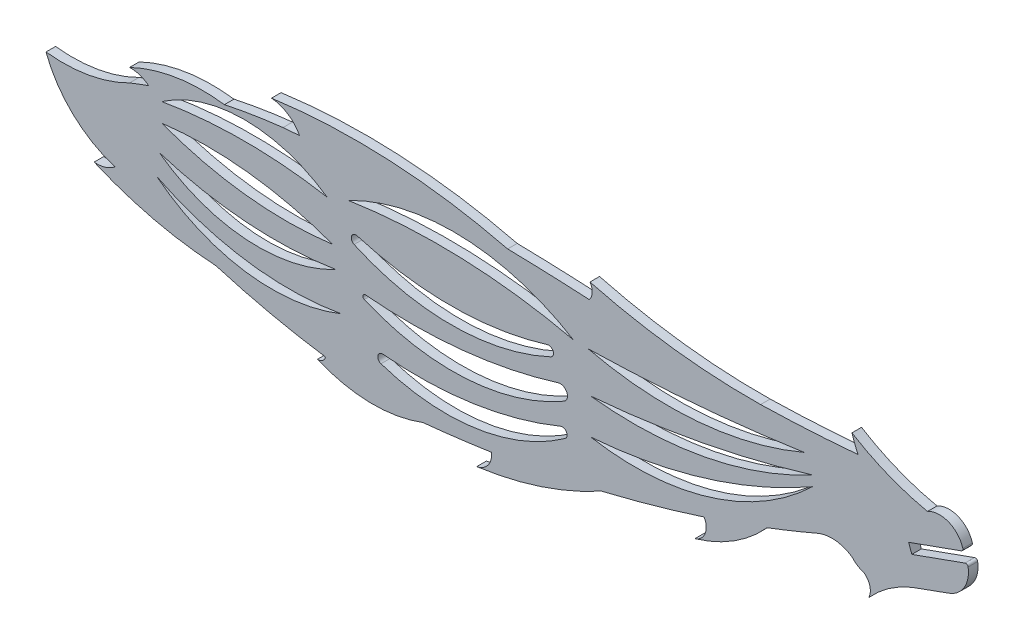
SolidWorks part; units mm, degrees
ref_plane "Front Plane" through (0, 0, 0) normal (0, 0, 1) x (1, 0, 0)
ref_plane "Top Plane" through (0, 0, 0) normal (0, 1, 0) x (1, 0, 0)
ref_plane "Right Plane" through (0, 0, 0) normal (1, 0, 0) x (0, 0, -1)
sketch "Model" plane through (0, 0, 0) normal (0, 0, 1) x (1, 0, 0)
  line L123 (134.9601, 18.3195) -> (129.2015, 16.2312)
  line L124 (129.2015, 20.778) -> (137.684, 23.8208)
  line L125 (137.0994, 25.2113) -> (128.693, 22.1962)
  line L127 (128.693, 22.1962) -> (129.2015, 20.778)
  arc A0 (131.7063, 27.9608) -> (119.655, 32.7944) centre (139.3783, 64.5287) cw
  arc A1 (119.655, 32.7944) -> (120.6241, 30.2797) centre (140.8446, 39.5163) ccw
  arc A2 (105.0839, 29.4139) -> (77.8778, 32.7353) centre (103.7063, 131.2147) cw
  arc A3 (77.8778, 32.7353) -> (77.7776, 30.2466) centre (76.1605, 31.5581) cw
  arc A4 (64.7497, 30.737) -> (27.0955, 32.7353) centre (40.7026, -66.6251) ccw
  arc A5 (27.0955, 32.7353) -> (31.5734, 29.7989) centre (26.6528, 27.1776) cw
  arc A6 (31.5734, 29.7989) -> (28.9288, 29.5886) centre (58.0674, -320.0647) ccw
  arc A7 (19.5882, 28.0822) -> (4.4589, 25.6613) centre (16.0799, 1.5221) ccw
  arc A8 (4.4589, 25.6613) -> (7.5081, 24.6603) centre (4.6423, 21.0751) cw
  arc A9 (7.5081, 24.6603) -> (4.4589, 23.5146) centre (39.3416, -64.6877) ccw
  arc A10 (113.3444, 22.1962) -> (77.9904, 11.3865) centre (85.0429, 51.5398) cw
  arc A11 (77.9904, 11.3865) -> (113.3444, 22.1962) centre (71.7807, 94.9153) ccw
  arc A12 (2.1294, 10.7511) -> (-8.8663, 21.1325) centre (7.298, 27.2394) cw
  arc A13 (-8.8663, 21.1325) -> (4.4589, 23.5146) centre (-6.1591, 44.4505) ccw
  arc A14 (113.3444, 23.8208) -> (77.9904, 17.0437) centre (84.8883, 76.6639) cw
  arc A15 (77.9904, 17.0437) -> (113.3444, 23.8208) centre (63.9998, 185.6329) ccw
  arc A16 (112.01, 26.2737) -> (77.6132, 23.3639) centre (90.401, 76.9568) cw
  arc A17 (112.01, 26.2737) -> (77.6132, 23.3639) centre (71.1125, 304.9632) cw
  arc A18 (73.9204, 9.1442) -> (44.5527, 4.7814) centre (54.9716, 35.6719) cw
  arc A19 (44.8676, 6.258) -> (44.5527, 4.7814) centre (44.7956, 5.5015) ccw
  arc A20 (73.9204, 9.1442) -> (73.1899, 10.4655) centre (73.4787, 9.7626) ccw
  arc A21 (73.7172, 14.1909) -> (72.8099, 16.2737) centre (73.1472, 15.1816) ccw
  arc A22 (42.0825, 13.0585) -> (41.8977, 12.3289) centre (42.0479, 12.6791) ccw
  arc A23 (71.616, 19.2633) -> (71.0698, 20.6822) centre (71.2941, 19.9539) ccw
  arc A24 (71.616, 19.2633) -> (40.2609, 19.1088) centre (55.7706, 53.2676) cw
  arc A25 (40.7931, 20.5331) -> (40.2609, 19.1088) centre (40.576, 19.8027) ccw
  arc A26 (75.2499, 23.4198) -> (39.3416, 24.7371) centre (53.8476, -69.9164) ccw
  arc A27 (38.2181, 8.5094) -> (8.7994, 12.7634) centre (29.9308, 55.0476) cw
  arc A28 (38.2181, 8.5094) -> (8.7994, 12.7634) centre (27.1804, 36.0274) cw
  arc A29 (37.3663, 14.1909) -> (9.1844, 16.2737) centre (27.7067, 75.191) cw
  arc A30 (75.2499, 23.4198) -> (39.3416, 24.7371) centre (56.1249, -7.8384) ccw
  arc A31 (37.3663, 14.1909) -> (9.1844, 16.2737) centre (24.9433, 37.8005) cw
  arc A32 (36.8481, 17.4136) -> (9.5963, 20.5331) centre (29.4735, 73.5855) cw
  arc A33 (36.8481, 17.4136) -> (9.5963, 20.5331) centre (16.7849, -37.2641) ccw
  arc A34 (35.9416, 23.5146) -> (9.5963, 23.5146) centre (22.7689, -52.3531) ccw
  arc A35 (9.5963, 23.5146) -> (35.9416, 23.5146) centre (22.7689, 4.4041) cw
  arc A36 (129.2015, 16.2312) -> (122.3426, 11.3865) centre (136.1962, -0.9492) ccw
  arc A37 (122.3426, 11.3865) -> (121.6378, 14.3951) centre (120.1266, 12.4542) ccw
  arc A38 (106.1164, 12.9157) -> (94.6123, 5.6577) centre (87.6223, 29.4831) cw
  arc A39 (94.6123, 5.6577) -> (96.0883, 9.3784) centre (93.8351, 8.1191) ccw
  arc A40 (79.7389, 4.7814) -> (59.8253, -1.7849) centre (52.2575, 54.6457) cw
  arc A41 (59.8253, -1.7849) -> (62.1772, 1.3676) centre (59.3236, 1.043) ccw
  arc A42 (51.2039, 0.0016) -> (34.4303, 0.3491) centre (43.2461, 20.8844) cw
  arc A43 (34.4303, 0.3491) -> (35.6963, 1.2959) centre (34.5272, 1.5393) ccw
  arc A44 (18.2423, 5.157) -> (-1.1865, 9.7626) centre (21.6438, 62.7892) cw
  arc A45 (-1.1865, 9.7626) -> (2.1294, 10.7511) centre (-0.749, 14.351) ccw
  arc A46 (79.7389, 4.7814) -> (96.0883, 9.3784) centre (30.4578, 211.4217) ccw
  arc A47 (106.1164, 12.9157) -> (114.1114, 16.1503) centre (30.4578, 211.4217) ccw
  arc A435 (137.3338, 25.6667) -> (131.7063, 27.9608) centre (133.6247, 24.6174) ccw
  arc A436 (77.7776, 30.2466) -> (64.7497, 30.737) centre (58.0674, -320.0647) ccw
  arc A437 (105.0839, 29.4139) -> (120.6241, 30.2797) centre (99.3935, 271.4491) ccw
  arc A442 (18.2423, 5.157) -> (35.6963, 1.2959) centre (53.7816, 124.4326) ccw
  arc A452 (28.9288, 29.5886) -> (19.5882, 28.0822) centre (39.3416, -64.6877) ccw
  arc A459 (51.2039, 0.0016) -> (62.1772, 1.3676) centre (30.4578, 211.4217) ccw
  arc A474 (44.8676, 6.258) -> (73.1899, 10.4655) centre (50.5196, 65.6398) ccw
  arc A475 (41.8977, 12.3289) -> (73.7172, 14.1909) centre (55.9455, 45.0791) ccw
  arc A476 (42.0825, 13.0585) -> (72.8099, 16.2737) centre (49.3189, 92.3376) ccw
  arc A477 (40.7931, 20.5331) -> (71.0698, 20.6822) centre (55.685, 70.6374) ccw
  arc A512 (119.655, 15.6682) -> (121.6378, 14.3951) centre (122.9089, 18.5551) ccw
  arc A515 (119.655, 15.6682) -> (114.1114, 16.1503) centre (116.4492, 10.9179) ccw
  arc A521 (134.9601, 18.3195) -> (138.1818, 23.523) centre (133.4993, 22.8231) ccw
  arc A645 (138.1818, 23.523) -> (137.684, 23.8208) centre (137.8107, 23.4676) ccw
  arc A646 (137.0994, 25.2113) -> (137.3338, 25.6667) centre (136.9727, 25.5645) ccw
  dimension "D1" = 1.143
  dimension "D2" = 0.381
  dimension "D3" = 0.762
  dimension "D4" = 0.762
extrude "Boss-Extrude1" add sketch "Model" along normal blind 1.524
